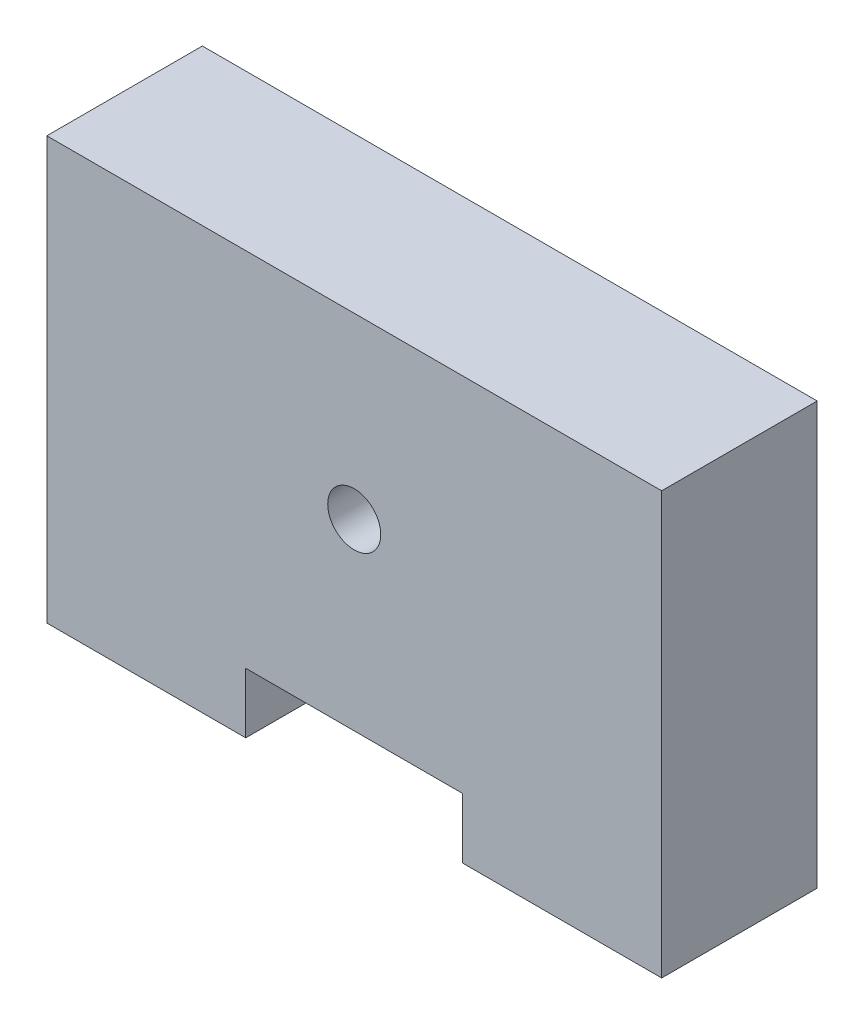
SolidWorks part; units mm, degrees
material "1060 Alloy"
ref_plane "Front Plane" through (0, 0, 0) normal (0, 0, 1) x (1, 0, 0)
ref_plane "Top Plane" through (0, 0, 0) normal (0, 1, 0) x (1, 0, 0)
ref_plane "Right Plane" through (0, 0, 0) normal (1, 0, 0) x (0, 0, -1)
sketch "Sketch2" plane through (0, 0, 0) normal (0, 1, 0) x (1, 0, 0)
  line L0 (25.5, 6.45) -> (-25.5, 6.45)
  line L1 (25.5, 6.45) -> (25.5, -6.45)
  line L2 (25.5, -6.45) -> (-25.5, -6.45)
  line L3 (-25.5, 6.45) -> (-25.5, -6.45)
  line L4 (-18.75, 0) -> (18.75, 0) construction
  point P0 (-18.75, 0)
  point P1 (18.75, 0)
  point P6 (-25.5, 0)
  point P9 (0, 0)
  point P13 (0, 6.45)
  dimension "D1" = 37.5
  dimension "D2" = 12.9
  dimension "D3" = 51
extrude "Boss-Extrude1" add sketch "Sketch2" along normal blind 35
hole_wizard "M3x0.5 Tapped Hole1" positions "Sketch3" profile "Sketch4" tap size "M3x0.5" standard "ANSI Metric"
sketch "Sketch3" plane through (0, 0, 0) normal (0, -1, 0) x (-1, 0, 0)
  point P0 (-18.75, 0)
  point P3 (18.75, 0)
sketch "Sketch4" plane through (18.75, 0, 0) normal (1, 0, 0) x (0, 0, -1)
  line L0 (0, 0) -> (0, 16.7511)
  line L1 (0, 16.7511) -> (1.25, 16)
  line L2 (1.25, 16) -> (1.25, 0)
  line L5 (1.25, 0) -> (0, 0)
  line L10 (0, 16.7511) -> (-1.25, 16) construction
  line L11 (0, -6.35) -> (0, 107.95) construction
  dimension "Tap Drill Dia." = 2.5
  dimension "Tap Drill Depth" = 16
  dimension "Drill Angle" = 118
cosmetic thread "Hole Thread1" parameters "D1"=6, "D2"=3
cosmetic thread "Hole Thread2" parameters "D1"=6, "D2"=3
sketch "Sketch5" plane through (0, 0, -6.45) normal (0, 0, -1) x (-1, 0, 0)
  line L0 (-25.5, 0) -> (25.5, 0) construction
  line L1 (-9, 0) -> (9, 0)
  line L2 (-9, 0) -> (-9, 5)
  line L3 (-9, 5) -> (9, 5)
  line L4 (9, 0) -> (9, 5)
  circle A0 centre (0, 20.2) radius 2.2
  point P6 (0, 0)
  dimension "D3" = 4.4
  dimension "D1" = 5
  dimension "D2" = 18
  dimension "D4" = 20.2
extrude "Cut-Extrude1" cut sketch "Sketch5" against normal up to surface (12.9 mm away) up to face at (0, 17.5, 6.45)
